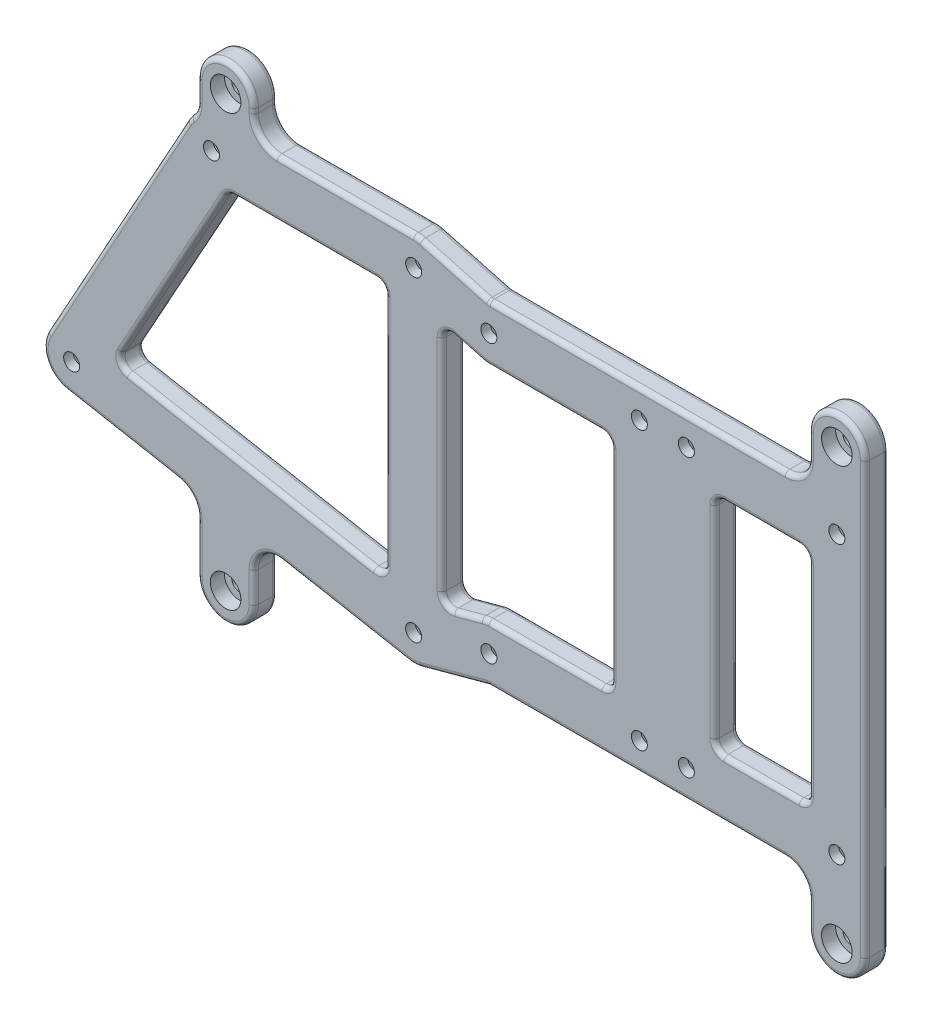
SolidWorks part; units mm, degrees
ref_plane "Plan de face" through (0, 0, 0) normal (0, 0, 1) x (1, 0, 0)
ref_plane "Plan de dessus" through (0, 0, 0) normal (0, 1, 0) x (1, 0, 0)
ref_plane "Plan de droite" through (0, 0, 0) normal (1, 0, 0) x (0, 0, -1)
sketch "Esquisse1" plane through (0, 0, 0) normal (0, 0, 1) x (1, 0, 0)
  line L0 (0, 33.625) -> (0, -33.625) construction
  line L1 (-43, 33.625) -> (0, 33.625) construction
  line L2 (0, -20.125) -> (-72.74, -20.125) construction
  line L3 (-1.0949, -39.5243) -> (-73.8349, -26.0243)
  line L4 (6, 33.625) -> (6, -33.625)
  line L5 (-43, 39.625) -> (0, 39.625)
  line L6 (-43, 27.625) -> (0, 27.625) construction
  line L7 (-48.25, 36.5298) -> (-77.99, -17.2202)
  line L8 (-37.75, 30.7202) -> (-67.49, -23.0298) construction
  line L9 (-6, 33.625) -> (-6, -33.625) construction
  line L10 (1.0949, -27.7257) -> (-71.6451, -14.2257) construction
  line L11 (-39.4626, 27.625) -> (-6, 27.625)
  line L12 (-6, 27.625) -> (-6, -26.409)
  line L13 (-6, -26.409) -> (-63.4593, -15.745)
  line L14 (-63.4593, -15.745) -> (-39.4626, 27.625)
  circle A0 centre (-43, 33.625) radius 1.7
  circle A2 centre (0, 33.625) radius 1.7
  circle A3 centre (0, -33.625) radius 1.7
  circle A4 centre (-72.74, -20.125) radius 1.7
  circle A5 centre (0, 33.625) radius 6 construction
  circle A6 centre (0, -33.625) radius 6 construction
  circle A7 centre (-72.74, -20.125) radius 6 construction
  circle A8 centre (-43, 33.625) radius 6 construction
  arc A9 (-48.25, 36.5298) -> (-43, 39.625) centre (-43, 33.625) cw
  arc A10 (0, 39.625) -> (6, 33.625) centre (0, 33.625) cw
  arc A11 (6, -33.625) -> (-1.0949, -39.5243) centre (0, -33.625) cw
  arc A12 (-77.99, -17.2202) -> (-73.8349, -26.0243) centre (-72.74, -20.125) ccw
  point P10 (0, 0)
  point P13 (-43, 33.625)
  dimension "D1" = 67.25
  dimension "D5" = 3.4
  dimension "12" = 12
  dimension "D2" = 43
  dimension "D3" = 72.74
  dimension "D4" = 13.5
extrude "Boss.-Extru.2" add sketch "Esquisse1" along normal blind 5
sketch "Esquisse2" plane through (0, 0, 5) normal (0, 0, 1) x (1, 0, 0)
  line L0 (0, 0) -> (16, 0) construction
  line L1 (16, 29.5) -> (48, 29.5) construction
  line L2 (16, 29.5) -> (16, -29.5) construction
  line L3 (16, -29.5) -> (48, -29.5) construction
  line L4 (48, 29.5) -> (48, -29.5) construction
  line L5 (58, 29.5) -> (90, 29.5) construction
  line L6 (58, 29.5) -> (58, -29.5) construction
  line L7 (58, -29.5) -> (90, -29.5) construction
  line L8 (90, 29.5) -> (90, -29.5) construction
  line L9 (48, 0) -> (58, 0) construction
  line L10 (58, 29.5) -> (90, -29.5) construction
  line L11 (16, 29.5) -> (48, -29.5) construction
  line L12 (16, 35.5) -> (90, 35.5)
  line L13 (12, -32.5) -> (52, -32.5) construction
  line L14 (12, -32.5) -> (12, 32.5) construction
  line L15 (12, 32.5) -> (52, 32.5) construction
  line L16 (52, -32.5) -> (52, 32.5) construction
  line L17 (12, -32.5) -> (52, 32.5) construction
  line L18 (12, 32.5) -> (52, -32.5) construction
  line L19 (54, -32.5) -> (94, -32.5) construction
  line L20 (54, -32.5) -> (54, 32.5) construction
  line L21 (54, 32.5) -> (94, 32.5) construction
  line L22 (94, -32.5) -> (94, 32.5) construction
  line L23 (54, -32.5) -> (94, 32.5) construction
  line L24 (54, 32.5) -> (94, -32.5) construction
  line L25 (96, 29.5) -> (96, -29.5)
  line L26 (16, -35.5) -> (90, -35.5)
  line L27 (84, 29.5) -> (84, -29.5) construction
  line L28 (64, 29.5) -> (64, -29.5) construction
  line L29 (42, 29.5) -> (42, -29.5) construction
  line L30 (90, -23.5) -> (58, -23.5) construction
  line L31 (58, 23.5) -> (90, 23.5) construction
  line L32 (64, 23.5) -> (84, 23.5)
  line L33 (84, 23.5) -> (84, -23.5)
  line L34 (84, -23.5) -> (64, -23.5)
  line L35 (64, -23.5) -> (64, 23.5)
  line L36 (14.4286, 23.7094) -> (6, 25.9967)
  line L37 (6, -33.625) -> (6, 33.625) construction
  line L38 (16, 35.5) -> (1.5714, 39.4156)
  line L39 (16, 23.5) -> (48, 23.5) construction
  line L40 (48, -23.5) -> (16, -23.5) construction
  line L41 (16, -35.5) -> (1.5714, -39.4156)
  line L42 (14.4286, -23.7094) -> (6, -25.9967)
  line L43 (16, 23.5) -> (42, 23.5)
  line L44 (42, 23.5) -> (42, -23.5)
  line L45 (42, -23.5) -> (16, -23.5)
  line L46 (6, 33.625) -> (6, 25.9967)
  line L47 (6, -25.9967) -> (6, -33.625)
  circle A0 centre (16, 29.5) radius 1.7
  circle A1 centre (48, 29.5) radius 1.7
  circle A2 centre (48, -29.5) radius 1.7
  circle A3 centre (16, -29.5) radius 1.7
  circle A4 centre (58, 29.5) radius 1.7
  circle A5 centre (90, 29.5) radius 1.7
  circle A6 centre (90, -29.5) radius 1.7
  circle A7 centre (58, -29.5) radius 1.7
  circle A8 centre (90, 29.5) radius 6 construction
  circle A9 centre (90, -29.5) radius 6 construction
  circle A10 centre (58, -29.5) radius 6 construction
  circle A11 centre (48, -29.5) radius 6 construction
  circle A12 centre (16, -29.5) radius 6 construction
  circle A13 centre (16, 29.5) radius 6 construction
  circle A14 centre (48, 29.5) radius 6 construction
  circle A15 centre (58, 29.5) radius 6 construction
  arc A16 (90, 35.5) -> (96, 29.5) centre (90, 29.5) cw
  arc A17 (96, -29.5) -> (90, -35.5) centre (90, -29.5) cw
  arc A18 (6, 33.625) -> (0, 39.625) centre (0, 33.625) ccw construction
  arc A19 (-1.0949, -39.5243) -> (6, -33.625) centre (0, -33.625) ccw construction
  arc A20 (14.4286, -23.7094) -> (16, -23.5) centre (16, -29.5) cw
  arc A21 (14.4286, 23.7094) -> (16, 23.5) centre (16, 29.5) ccw
  arc A22 (1.5714, -39.4156) -> (6, -33.625) centre (0, -33.625) ccw
  arc A23 (1.5714, 39.4156) -> (6, 33.625) centre (0, 33.625) cw
  point P21 (32, 0)
  point P26 (74, 0)
  dimension "D3" = 3.4
  dimension "D6" = 3.4
  dimension "D11" = 12
  dimension "D1" = 32
  dimension "D2" = 59
  dimension "D4" = 32
  dimension "D5" = 59
  dimension "D7" = 40
  dimension "D8" = 65
  dimension "D9" = 2
  dimension "D10" = 12
extrude "Boss.-Extru.3" add sketch "Esquisse2" against normal up to surface (5 mm away) up to face at (1.7, -33.625, 0)
fillet "Congé1" radius 2 14 edges at (16, 35.5, 2.5) (64, -23.5, 2.5) (16, -35.5, 2.5) (64, 23.5, 2.5) (84, 23.5, 2.5) (84, -23.5, 2.5) (42, -23.5, 2.5) (42, 23.5, 2.5) (6, 25.9967, 2.5) (6, -25.9967, 2.5) (-6, -26.409, 2.5) (-6, 27.625, 2.5) (-63.4593, -15.745, 2.5) (-39.4626, 27.625, 2.5)
sketch "Esquisse4" plane through (0, 0, 5) normal (0, 0, 1) x (1, 0, 0)
  line L0 (96, 0) -> (84, 0) construction
  line L1 (96, -29.5) -> (96, 29.5) construction
  line L2 (84, -21.5) -> (84, 21.5) construction
  line L3 (90, 45.625) -> (90, -45.9173) construction
  line L4 (90, 45.625) -> (-40, 45.625) construction
  line L5 (-40, 45.625) -> (-40, -45.9173) construction
  line L6 (-40, -45.9173) -> (90, -45.9173) construction
  line L7 (96, 45.625) -> (96, 29.5)
  line L8 (84, 45.625) -> (84, 35.5)
  line L11 (90, 35.5) -> (16.2666, 35.5) construction
  line L12 (96, -45.9173) -> (96, -29.5)
  line L13 (84, -45.9173) -> (84, -35.5)
  line L16 (16.2666, -35.5) -> (90, -35.5) construction
  line L17 (-34, 45.625) -> (-34, 39.625)
  line L18 (0, 39.625) -> (-43, 39.625) construction
  line L19 (-46, 45.625) -> (-46, 38.8212)
  line L20 (-34, -45.9173) -> (-34, -33.4173)
  line L21 (-73.8349, -26.0243) -> (-1.0949, -39.5243) construction
  line L22 (-46, -45.9173) -> (-46, -31.1902)
  line L23 (-46, 38.8212) -> (-34, 39.625)
  line L24 (84, 35.5) -> (96, 29.5)
  line L25 (-46, -31.1902) -> (-34, -33.4173)
  line L26 (84, -35.5) -> (96, -29.5)
  circle A0 centre (90, 45.625) radius 1.7
  circle A1 centre (90, -45.9173) radius 1.7
  circle A2 centre (-40, 45.625) radius 1.7
  circle A3 centre (-40, -45.9173) radius 1.7
  circle A4 centre (-40, 45.625) radius 6 construction
  circle A5 centre (90, 45.625) radius 6 construction
  circle A6 centre (90, -45.9173) radius 6 construction
  circle A7 centre (-40, -45.9173) radius 6 construction
  arc A9 (-46, 45.625) -> (-34, 45.625) centre (-40, 45.625) cw
  arc A10 (-43, 39.625) -> (-48.25, 36.5298) centre (-43, 33.625) ccw construction
  arc A11 (84, 45.625) -> (96, 45.625) centre (90, 45.625) cw
  arc A12 (-46, -45.9173) -> (-34, -45.9173) centre (-40, -45.9173) ccw
  arc A13 (84, -45.9173) -> (96, -45.9173) centre (90, -45.9173) ccw
  point P9 (90, 0)
  dimension "D1" = 3.4
  dimension "D2" = 130
  dimension "D3" = 12
  dimension "D4" = 12.5
extrude "Boss.-Extru.4" add sketch "Esquisse4" against normal up to surface (5 mm away) up to face at (12.1756, 2.0354, 0)
sketch "Esquisse3" plane through (0, 0, 0) normal (0, 0, -1) x (-1, 0, 0)
  line L0 (-91.6454, -26.65) -> (-88.3546, -26.65)
  line L1 (-88.3546, -26.65) -> (-86.7091, -29.5)
  line L2 (-86.7091, -29.5) -> (-88.3546, -32.35)
  line L3 (-88.3546, -32.35) -> (-91.6454, -32.35)
  line L4 (-91.6454, -32.35) -> (-93.2909, -29.5)
  line L5 (-93.2909, -29.5) -> (-91.6454, -26.65)
  line L6 (-93.2909, -29.5) -> (-86.7091, -29.5) construction
  line L7 (-91.6454, 32.35) -> (-88.3546, 32.35)
  line L8 (-88.3546, 32.35) -> (-86.7091, 29.5)
  line L9 (-86.7091, 29.5) -> (-88.3546, 26.65)
  line L10 (-88.3546, 26.65) -> (-91.6454, 26.65)
  line L11 (-91.6454, 26.65) -> (-93.2909, 29.5)
  line L12 (-93.2909, 29.5) -> (-91.6454, 32.35)
  line L13 (-93.2909, 29.5) -> (-86.7091, 29.5) construction
  line L14 (-59.6454, 32.35) -> (-56.3546, 32.35)
  line L15 (-56.3546, 32.35) -> (-54.7091, 29.5)
  line L16 (-54.7091, 29.5) -> (-56.3546, 26.65)
  line L17 (-56.3546, 26.65) -> (-59.6454, 26.65)
  line L18 (-59.6454, 26.65) -> (-61.2909, 29.5)
  line L19 (-61.2909, 29.5) -> (-59.6454, 32.35)
  line L20 (-61.2909, 29.5) -> (-54.7091, 29.5) construction
  line L21 (-49.6454, 32.35) -> (-46.3546, 32.35)
  line L22 (-46.3546, 32.35) -> (-44.7091, 29.5)
  line L23 (-44.7091, 29.5) -> (-46.3546, 26.65)
  line L24 (-46.3546, 26.65) -> (-49.6454, 26.65)
  line L25 (-49.6454, 26.65) -> (-51.2909, 29.5)
  line L26 (-51.2909, 29.5) -> (-49.6454, 32.35)
  line L27 (-51.2909, 29.5) -> (-44.7091, 29.5) construction
  line L28 (-59.6454, -26.65) -> (-56.3546, -26.65)
  line L29 (-56.3546, -26.65) -> (-54.7091, -29.5)
  line L30 (-54.7091, -29.5) -> (-56.3546, -32.35)
  line L31 (-56.3546, -32.35) -> (-59.6454, -32.35)
  line L32 (-59.6454, -32.35) -> (-61.2909, -29.5)
  line L33 (-61.2909, -29.5) -> (-59.6454, -26.65)
  line L34 (-61.2909, -29.5) -> (-54.7091, -29.5) construction
  line L35 (-49.6454, -26.65) -> (-46.3546, -26.65)
  line L36 (-46.3546, -26.65) -> (-44.7091, -29.5)
  line L37 (-44.7091, -29.5) -> (-46.3546, -32.35)
  line L38 (-46.3546, -32.35) -> (-49.6454, -32.35)
  line L39 (-49.6454, -32.35) -> (-51.2909, -29.5)
  line L40 (-51.2909, -29.5) -> (-49.6454, -26.65)
  line L41 (-51.2909, -29.5) -> (-44.7091, -29.5) construction
  line L42 (-17.6454, -26.65) -> (-14.3546, -26.65)
  line L43 (-14.3546, -26.65) -> (-12.7091, -29.5)
  line L44 (-12.7091, -29.5) -> (-14.3546, -32.35)
  line L45 (-14.3546, -32.35) -> (-17.6454, -32.35)
  line L46 (-17.6454, -32.35) -> (-19.2909, -29.5)
  line L47 (-19.2909, -29.5) -> (-17.6454, -26.65)
  line L48 (-19.2909, -29.5) -> (-12.7091, -29.5) construction
  line L49 (-1.6454, -30.775) -> (1.6454, -30.775)
  line L50 (1.6454, -30.775) -> (3.2909, -33.625)
  line L51 (3.2909, -33.625) -> (1.6454, -36.475)
  line L52 (1.6454, -36.475) -> (-1.6454, -36.475)
  line L53 (-1.6454, -36.475) -> (-3.2909, -33.625)
  line L54 (-3.2909, -33.625) -> (-1.6454, -30.775)
  line L55 (-3.2909, -33.625) -> (3.2909, -33.625) construction
  line L56 (-17.6454, 32.35) -> (-14.3546, 32.35)
  line L57 (-14.3546, 32.35) -> (-12.7091, 29.5)
  line L58 (-12.7091, 29.5) -> (-14.3546, 26.65)
  line L59 (-14.3546, 26.65) -> (-17.6454, 26.65)
  line L60 (-17.6454, 26.65) -> (-19.2909, 29.5)
  line L61 (-19.2909, 29.5) -> (-17.6454, 32.35)
  line L62 (-19.2909, 29.5) -> (-12.7091, 29.5) construction
  line L63 (-1.6454, 36.475) -> (1.6454, 36.475)
  line L64 (1.6454, 36.475) -> (3.2909, 33.625)
  line L65 (3.2909, 33.625) -> (1.6454, 30.775)
  line L66 (1.6454, 30.775) -> (-1.6454, 30.775)
  line L67 (-1.6454, 30.775) -> (-3.2909, 33.625)
  line L68 (-3.2909, 33.625) -> (-1.6454, 36.475)
  line L69 (-3.2909, 33.625) -> (3.2909, 33.625) construction
  line L70 (41.3546, 36.475) -> (44.6454, 36.475)
  line L71 (44.6454, 36.475) -> (46.2909, 33.625)
  line L72 (46.2909, 33.625) -> (44.6454, 30.775)
  line L73 (44.6454, 30.775) -> (41.3546, 30.775)
  line L74 (41.3546, 30.775) -> (39.7091, 33.625)
  line L75 (39.7091, 33.625) -> (41.3546, 36.475)
  line L76 (39.7091, 33.625) -> (46.2909, 33.625) construction
  line L77 (71.0946, -17.275) -> (74.3854, -17.275)
  line L78 (74.3854, -17.275) -> (76.0309, -20.125)
  line L79 (76.0309, -20.125) -> (74.3854, -22.975)
  line L80 (74.3854, -22.975) -> (71.0946, -22.975)
  line L81 (71.0946, -22.975) -> (69.4491, -20.125)
  line L82 (69.4491, -20.125) -> (71.0946, -17.275)
  line L83 (69.4491, -20.125) -> (76.0309, -20.125) construction
  point P0 (-90, 29.5)
  point P1 (-90, -29.5)
  point P3 (-48, -29.5)
  point P5 (-58, -29.5)
  point P7 (-58, 29.5)
  point P9 (-48, 29.5)
  point P11 (-16, 29.5)
  point P13 (-16, -29.5)
  point P15 (0, -33.625)
  point P17 (0, 33.625)
  point P19 (43, 33.625)
  point P21 (72.74, -20.125)
  point P23 (-90, -29.5)
  point P25 (-90, -29.5)
  point P28 (-90, -29.5)
  point P33 (-90, -29.5)
  point P34 (-90, 29.5)
  point P35 (-90, 29.5)
  point P38 (-90, 29.5)
  point P43 (-90, 29.5)
  point P44 (-58, 29.5)
  point P45 (-58, 29.5)
  point P48 (-58, 29.5)
  point P53 (-58, 29.5)
  point P54 (-48, 29.5)
  point P55 (-48, 29.5)
  point P58 (-48, 29.5)
  point P63 (-48, 29.5)
  point P64 (0, 0)
  point P65 (0, 0)
  point P66 (0, 0)
  point P67 (0, 0)
  point P68 (-58, -29.5)
  point P69 (-58, -29.5)
  point P72 (-58, -29.5)
  point P77 (-58, -29.5)
  point P78 (-48, -29.5)
  point P79 (-48, -29.5)
  point P82 (-48, -29.5)
  point P87 (-48, -29.5)
  point P88 (0, 0)
  point P89 (0, 0)
  point P90 (-16, -29.5)
  point P91 (-16, -29.5)
  point P94 (-16, -29.5)
  point P99 (-16, -29.5)
  point P100 (0, -33.625)
  point P101 (0, -33.625)
  point P104 (0, -33.625)
  point P109 (0, -33.625)
  point P110 (0, 0)
  point P111 (0, 0)
  point P112 (-16, 29.5)
  point P113 (-16, 29.5)
  point P116 (-16, 29.5)
  point P121 (-16, 29.5)
  point P122 (0, 33.625)
  point P123 (0, 33.625)
  point P126 (0, 33.625)
  point P131 (0, 33.625)
  point P132 (0, 0)
  point P133 (0, 0)
  point P134 (43, 33.625)
  point P135 (43, 33.625)
  point P138 (43, 33.625)
  point P143 (43, 33.625)
  point P144 (0, 0)
  point P145 (72.74, -20.125)
  point P146 (72.74, -20.125)
  point P149 (72.74, -20.125)
  point P154 (72.74, -20.125)
  point P155 (0, 0)
  dimension "D1" = 120
  dimension "D2" = 5.7
  dimension "D3" = 120
  dimension "D4" = 5.7
  dimension "D5" = 120
  dimension "D6" = 5.7
  dimension "D7" = 120
  dimension "D8" = 5.7
  dimension "D9" = 120
  dimension "D10" = 5.7
  dimension "D11" = 120
  dimension "D12" = 5.7
  dimension "D13" = 120
  dimension "D14" = 5.7
  dimension "D15" = 120
  dimension "D16" = 5.7
  dimension "D17" = 120
  dimension "D18" = 5.7
  dimension "D19" = 120
  dimension "D20" = 5.7
  dimension "D21" = 120
  dimension "D22" = 5.7
  dimension "D23" = 120
  dimension "D24" = 5.7
extrude "Enlèv. mat.-Extru.1" cut sketch "Esquisse3" against normal offset from surface (3 mm away) 2 up to face at (2.8636, 0.2019, 5)
fillet "Congé2" radius 5 6 edges at (-46, -31.1902, 2.5) (-34, -33.4173, 2.5) (84, -35.5, 2.5) (84, 35.5, 2.5) (-46, 38.8212, 2.5) (-34, 39.625, 2.5)
sketch "Esquisse5" plane through (0, 0, 5) normal (0, 0, 1) x (1, 0, 0)
  circle A0 centre (-40, 45.625) radius 3.25
  circle A1 centre (-40, -45.9173) radius 3.25
  circle A2 centre (90, -45.9173) radius 3.25
  circle A3 centre (90, 45.625) radius 3.25
  point P12 (-40, -45.9173)
  dimension "D1" = 6.5
extrude "Enlèv. mat.-Extru.2" cut sketch "Esquisse5" against normal offset from surface (3 mm away) 2 up to face at (48, -29.5, 0)
fillet "Congé3" radius 1 118 edges at (83.4142, -22.9142, 0) (83.4142, -22.9142, 5) (74, -23.5, 0) (74, -23.5, 5) (64.5858, -22.9142, 0) (64.5858, -22.9142, 5) (64, 0, 5) (64, 0, 0) (64.5858, 22.9142, 0) (64.5858, 22.9142, 5) (74, 23.5, 5) (74, 23.5, 0) (83.4142, 22.9142, 0) (83.4142, 22.9142, 5) (41.4142, 22.9142, 0) (41.4142, 22.9142, 5) (28, 23.5, 0) (28, 23.5, 5) (15.2073, 23.5526, 0) (15.2073, 23.5526, 5) (11.4762, 24.5106, 5) (11.4762, 24.5106, 0) (6.785, 24.9703, 0) (6.785, 24.9703, 5) (6, 0, 0) (6, 0, 5) (6.785, -24.9703, 0) (6.785, -24.9703, 5) (11.4762, -24.5106, 0) (11.4762, -24.5106, 5) (15.2073, -23.5526, 0) (15.2073, -23.5526, 5) (28, -23.5, 5) (28, -23.5, 0) (41.4142, -22.9142, 0) (41.4142, -22.9142, 5) (-6.7213, -25.5415, 5) (-6.7213, -25.5415, 0) (-34.5478, -21.1107, 5) (-34.5478, -21.1107, 0) (-62.1744, -15.1386, 5) (-62.1744, -15.1386, 0) (-51.0746, 6.6383, 5) (-51.0746, 6.6383, 0) (-39.2992, 27.3479, 5) (-39.2992, 27.3479, 0) (-23.1417, 27.625, 0) (-23.1417, 27.625, 5) (-6.5858, 27.0392, 5) (-6.5858, 27.0392, 0) (-47.8449, 37.1643, 5) (-47.8449, 37.1643, 0) (-46.3534, 39.3285, 0) (-46.3534, 39.3285, 5) (-46, 43.3999, 0) (-46, 43.3999, 5) (-40, 51.625, 0) (-40, 51.625, 5) (-34, 45.125, 5) (-34, 45.125, 0) (-32.5355, 41.0895, 0) (-32.5355, 41.0895, 5) (-14.5, 39.625, 0) (-14.5, 39.625, 5) (0.7927, 39.5724, 5) (0.7927, 39.5724, 0) (8.6571, 37.4927, 5) (8.6571, 37.4927, 0) (16.0023, 35.5175, 0) (16.0023, 35.5175, 5) (47.6333, 35.5, 5) (47.6333, 35.5, 0) (82.5355, 36.9645, 0) (82.5355, 36.9645, 5) (84, 43.0625, 0) (84, 43.0625, 5) (90, 51.625, 0) (90, 51.625, 5) (96, -0.1462, 5) (96, -0.1462, 0) (90, -51.9173, 0) (90, -51.9173, 5) (84, -43.2087, 5) (84, -43.2087, 0) (82.5355, -36.9645, 0) (82.5355, -36.9645, 5) (47.6333, -35.5, 0) (47.6333, -35.5, 5) (16.0023, -35.5175, 0) (16.0023, -35.5175, 5) (8.6571, -37.4927, 0) (8.6571, -37.4927, 5) (0.2444, -39.62, 5) (0.2444, -39.62, 0) (-14.5912, -37.0194, 5) (-14.5912, -37.0194, 0) (-32.1967, -35.5861, 0) (-32.1967, -35.5861, 5) (-34, -42.674, 0) (-34, -42.674, 5) (-40, -51.9173, 0) (-40, -51.9173, 5) (-46, -40.6325, 5) (-46, -40.6325, 0) (-47.1554, -32.1509, 0) (-47.1554, -32.1509, 5) (-61.9612, -28.2279, 0) (-61.9612, -28.2279, 5) (-78.1661, -22.6858, 0) (-78.1661, -22.6858, 5) (-63.12, 9.6548, 0) (-63.12, 9.6548, 5) (84, 0, 5) (84, 0, 0) (42, 0, 0) (42, 0, 5) (-6, 0.8107, 0) (-6, 0.8107, 5)
